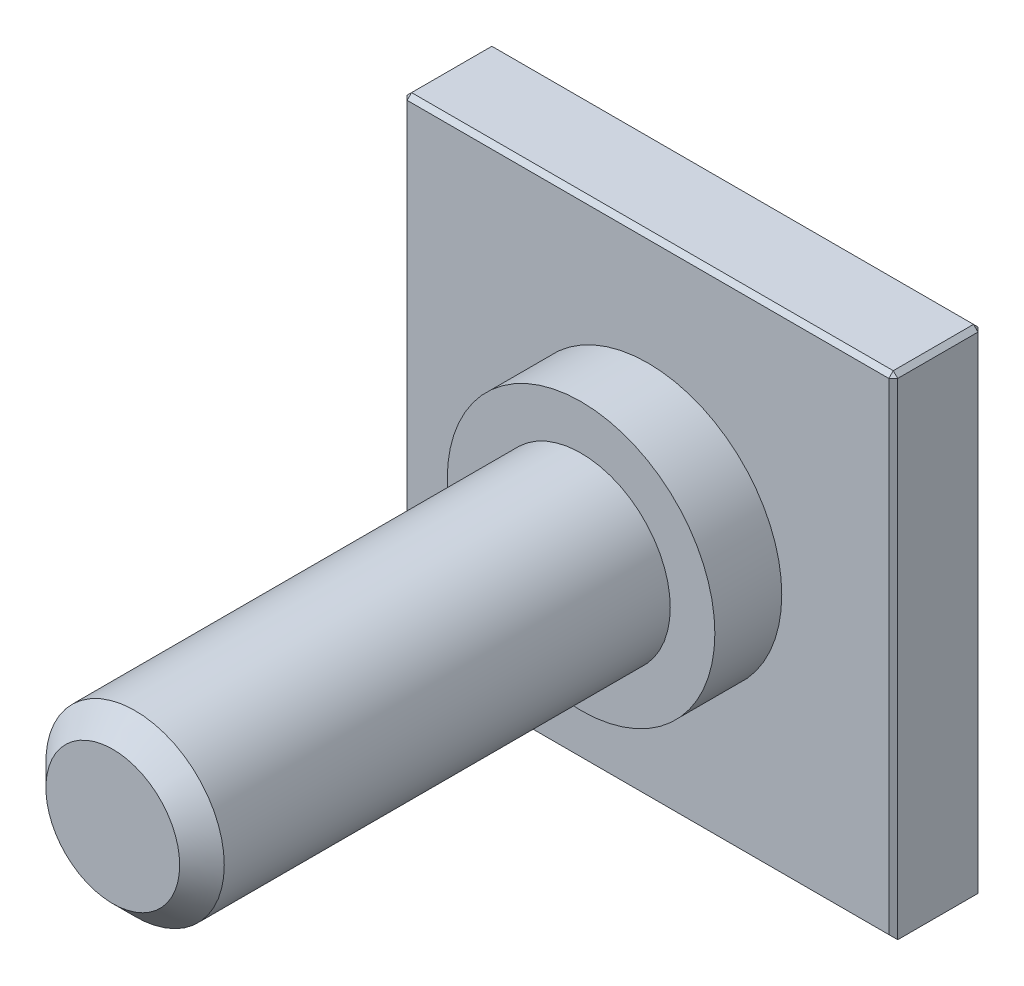
SolidWorks part; units mm, degrees
ref_plane "Front Plane" through (0, 0, 0) normal (0, 0, 1) x (1, 0, 0)
ref_plane "Top Plane" through (0, 0, 0) normal (0, 1, 0) x (1, 0, 0)
ref_plane "Right Plane" through (0, 0, 0) normal (1, 0, 0) x (0, 0, -1)
sketch "Sketch1" plane through (0, 0, 0) normal (0, 0, 1) x (1, 0, 0)
  line L1 (-5.5, -5.5) -> (5.5, -5.5)
  line L2 (-5.5, -5.5) -> (-5.5, 5.5)
  line L3 (-5.5, 5.5) -> (5.5, 5.5)
  line L4 (5.5, -5.5) -> (5.5, 5.5)
  line L5 (-5.5, -5.5) -> (5.5, 5.5) construction
  line L6 (-5.5, 5.5) -> (5.5, -5.5) construction
  point P0 (0, 0)
  dimension "D1" = 11
  dimension "D2" = 11
extrude "Boss-Extrude1" add sketch "Sketch1" along normal blind 2
sketch "Sketch2" plane through (0, 0, 2) normal (0, 0, 1) x (1, 0, 0)
  circle A0 centre (0, 0) radius 2
  dimension "D1" = 4
extrude "Boss-Extrude2" add sketch "Sketch2" along normal blind 12
chamfer "Chamfer1" distance 0.1 angle 45 10 edges at (-5.5, 0, 0) (0, -5.5, 0) (5.5, 0, 0) (-5.5, 0, 2) (0, -5.5, 2) (5.5, 0, 2) (5.5, 5.5, 1) (0, 5.5, 2) (0, 5.5, 0) (-5.5, 5.5, 1)
sketch "Sketch3" plane through (0, 0, 2) normal (0, 0, 1) x (1, 0, 0)
  circle A0 centre (0, 0) radius 3
  dimension "D1" = 6
extrude "Boss-Extrude3" add sketch "Sketch3" along normal blind 1.5
chamfer "Chamfer2" distance 0.5 angle 45 1 edges at (2, 0, 14)
